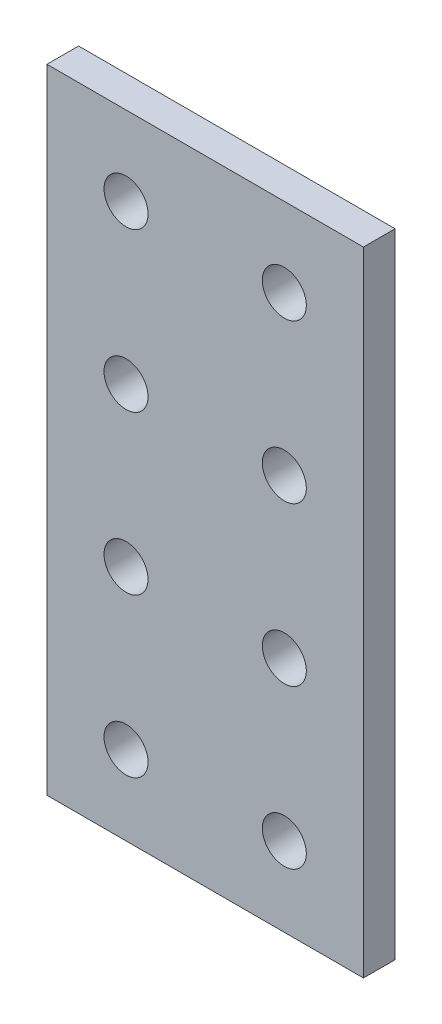
SolidWorks part; units mm, degrees
ref_plane "Front Plane" through (0, 0, 0) normal (0, 0, 1) x (1, 0, 0)
ref_plane "Top Plane" through (0, 0, 0) normal (0, 1, 0) x (1, 0, 0)
ref_plane "Right Plane" through (0, 0, 0) normal (1, 0, 0) x (0, 0, -1)
ref_plane "Plane1" through (0, 0, 4) normal (0, 0, 1) x (1, 0, 0)
sketch "Sketch1" plane through (0, 0, 4) normal (0, 0, 1) x (1, 0, 0)
  line L0 (20, 80) -> (-20, 80)
  line L1 (-20, 80) -> (-20, 0)
  line L2 (-20, 0) -> (20, 0)
  line L3 (20, 0) -> (20, 80)
  circle A0 centre (-10, 70) radius 2.78
  circle A1 centre (-10, 50) radius 2.78
  circle A2 centre (-10, 30) radius 2.78
  circle A3 centre (-10, 10) radius 2.78
  circle A4 centre (10, 70) radius 2.78
  circle A5 centre (10, 50) radius 2.78
  circle A6 centre (10, 30) radius 2.78
  circle A7 centre (10, 10) radius 2.78
extrude "Boss-Extrude1" add sketch "Sketch1" against normal blind 4
